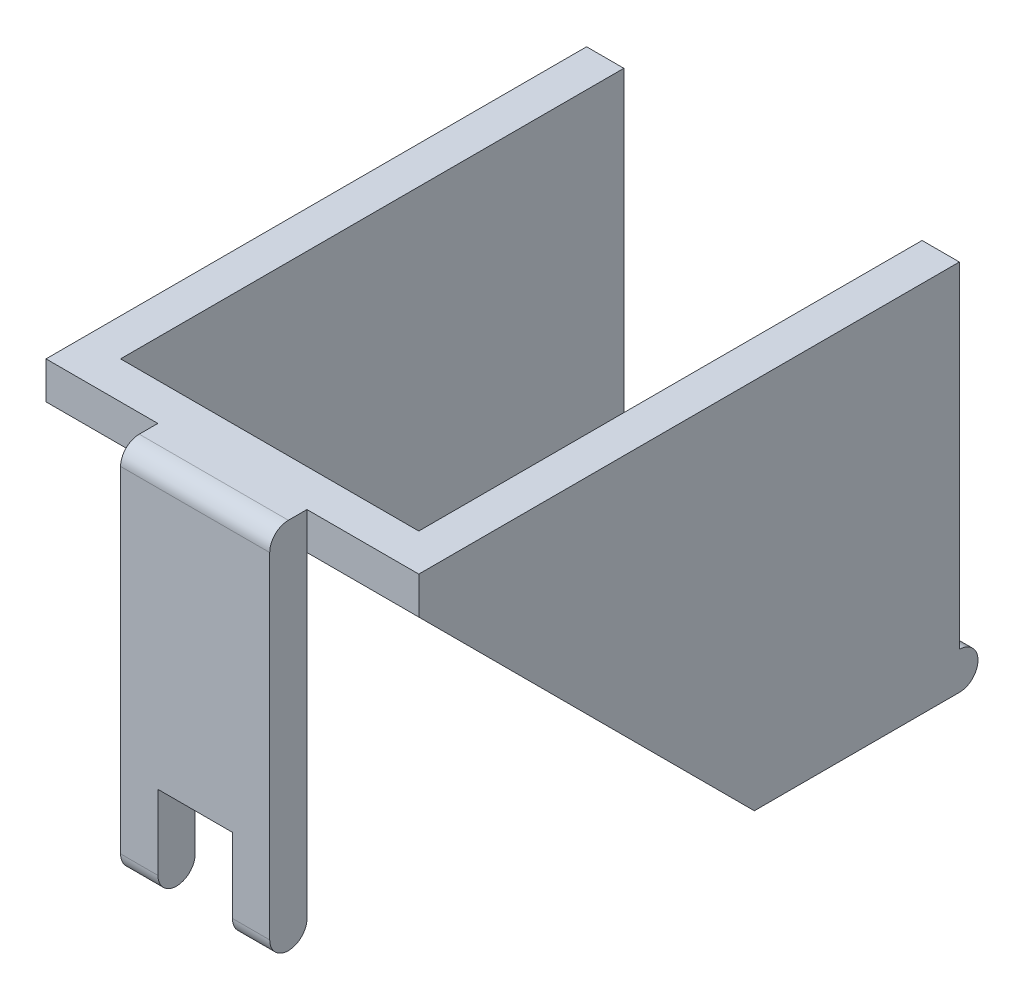
SolidWorks part; units mm, degrees
ref_plane "Front" through (0, 0, 0) normal (0, 0, 1) x (1, 0, 0)
ref_plane "Top" through (0, 0, 0) normal (0, 1, 0) x (1, 0, 0)
ref_plane "Right" through (0, 0, 0) normal (1, 0, 0) x (0, 0, -1)
sketch "草图3" plane through (0, 0, 0) normal (1, 0, 0) x (0, 0, -1)
  line L0 (-14.2929, 8.2929) -> (4, -10)
  line L1 (-15, 10) -> (15, 10)
  line L3 (4, -10) -> (15, -10)
  line L4 (15, 10) -> (15, -10)
  arc A0 (-15, 10) -> (-14.2929, 8.2929) centre (-15, 9) ccw
  dimension "D2" = 20
  dimension "D3" = 15
  dimension "D4" = 10
extrude "凸台-拉伸3" add sketch "草图3" along normal blind 20
sketch "草图4" plane through (0, 10, 0) normal (0, 1, 0) x (1, 0, 0)
  line L0 (20, 15) -> (20, -15) construction
  line L1 (0, -16) -> (6, -16)
  line L2 (0, -16) -> (0, -14.0026)
  line L3 (0, -14.0026) -> (6, -14.0026)
  line L4 (20, -16) -> (20, -14.0026)
  line L5 (6, -14.0026) -> (6, -16)
  line L6 (14, -14.0026) -> (14, -16)
  line L7 (14, -14.0026) -> (20, -14.0026)
  line L8 (14, -16) -> (20, -16)
  dimension "D1" = 6
  dimension "D2" = 6
extrude "切除-拉伸1" cut sketch "草图4" against normal blind 20
sketch "草图5" plane through (14, 0, 0) normal (1, 0, 0) x (0, 0, -1)
  line L0 (-15, 9) -> (-15, -10.4374) construction
  line L1 (-15, 9) -> (-15, -9) construction
  line L2 (-14, 9) -> (-14, -9)
  line L3 (-16, 9) -> (-16, -9)
  arc A0 (-14, 9) -> (-16, 9) centre (-15, 9) ccw
  arc A1 (-16, -9) -> (-14, -9) centre (-15, -9) ccw
  point P3 (-15, 0)
extrude "凸台-拉伸4" add sketch "草图5" against normal blind 8
sketch "草图6" plane through (20, 0, 0) normal (1, 0, 0) x (0, 0, -1)
  line L0 (15, -10) -> (15, 10) construction
  circle A0 centre (15, -9) radius 1
extrude "凸台-拉伸5" add sketch "草图6" against normal blind 20
sketch "草图7" plane through (0, 10, 0) normal (0, 1, 0) x (1, 0, 0)
  line L1 (2, 16.675) -> (18, 16.675)
  line L2 (2, 16.675) -> (2, -12.0026)
  line L3 (2, -12.0026) -> (18, -12.0026)
  line L4 (18, 16.675) -> (18, -12.0026)
  line L5 (10, -16) -> (10, 19.9119) construction
  line L6 (6, -16) -> (14, -16) construction
  line L7 (20, -14.0026) -> (14, -14.0026) construction
  dimension "D1" = 16
  dimension "D2" = 8
  dimension "D3" = 2
extrude "切除-拉伸3" cut sketch "草图7" against normal blind 18
sketch "草图8" plane through (0, 0, 16) normal (0, 0, 1) x (1, 0, 0)
  line L0 (10, -10) -> (10, 16.9603) construction
  line L1 (8, -5) -> (12, -5)
  line L2 (8, -5) -> (8, -11.3652)
  line L3 (8, -11.3652) -> (12, -11.3652)
  line L4 (12, -5) -> (12, -11.3652)
  line L5 (6, -10) -> (14, -10) construction
  line L6 (6, -9) -> (14, -9) construction
  dimension "D1" = 4
  dimension "D2" = 2
  dimension "D3" = 4
extrude "切除-拉伸4" cut sketch "草图8" against normal blind 10
sketch "草图9" plane through (0, -8, 0) normal (0, 1, 0) x (1, 0, 0)
  line L0 (10, 16) -> (10, -19.9158) construction
  line L1 (20, 16) -> (0, 16) construction
  line L3 (6, 16) -> (14, 16)
  line L4 (6, 16) -> (6, 12)
  line L5 (6, 12) -> (14, 12)
  line L6 (14, 16) -> (14, 12)
  dimension "D1" = 4
  dimension "D2" = 8
  dimension "D3" = 4
extrude "切除-拉伸5" cut sketch "草图9" against normal blind 10
